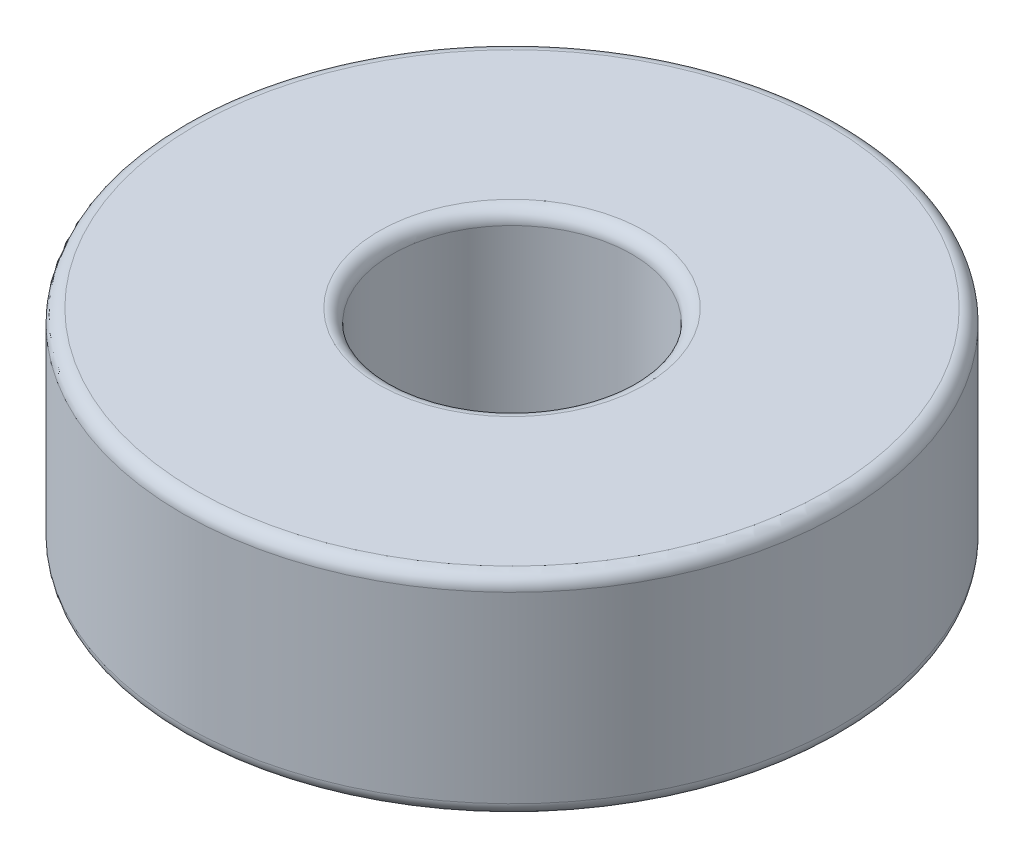
SolidWorks part; units mm, degrees
ref_plane "Front Plane" through (0, 0, 0) normal (0, 0, 1) x (1, 0, 0)
ref_plane "Top Plane" through (0, 0, 0) normal (0, 1, 0) x (1, 0, 0)
ref_plane "Right Plane" through (0, 0, 0) normal (1, 0, 0) x (0, 0, -1)
sketch "Sketch1" plane through (0, 0, 0) normal (0, 1, 0) x (1, 0, 0)
  circle A0 centre (0, 0) radius 11
  circle A1 centre (0, 0) radius 4
  dimension "D1" = 22
  dimension "D2" = 8
extrude "Boss-Extrude1" add sketch "Sketch1" along normal blind 7
fillet "Fillet1" radius 0.4445 4 edges at (0, 0, 4) (0, 0, 11) (0, 7, 4) (0, 7, 11)
